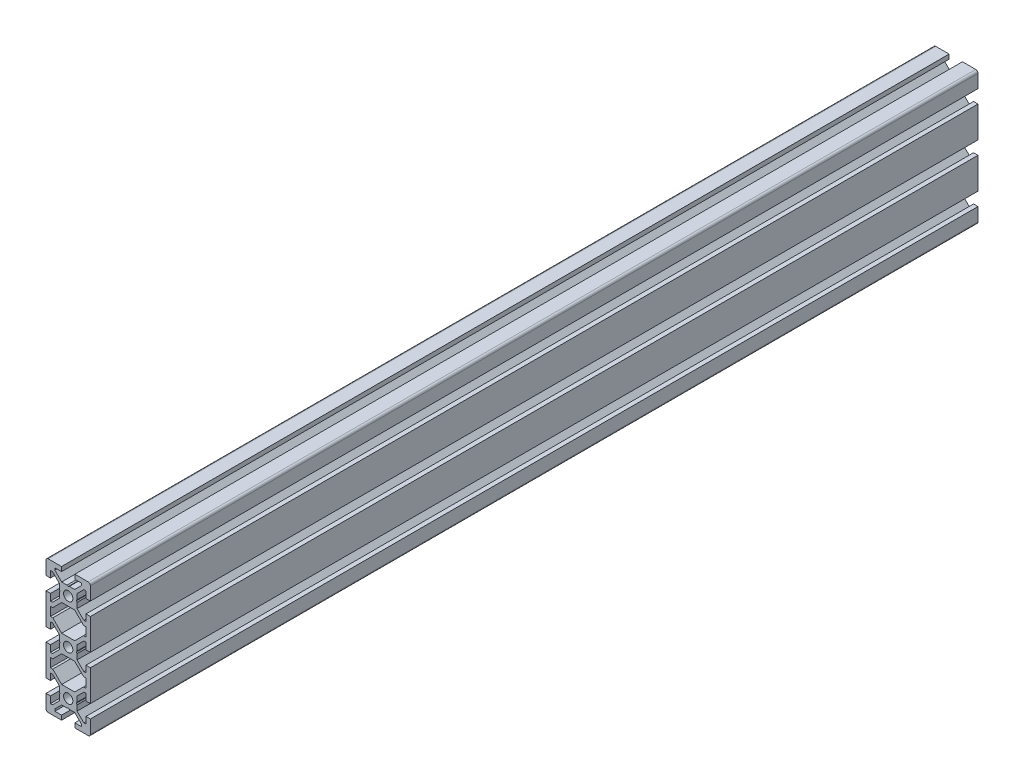
SolidWorks part; units mm, degrees
ref_plane "Front Plane" through (0, 0, 0) normal (0, 0, 1) x (1, 0, 0)
ref_plane "Top Plane" through (0, 0, 0) normal (0, 1, 0) x (1, 0, 0)
ref_plane "Right Plane" through (0, 0, 0) normal (1, 0, 0) x (0, 0, -1)
ref_plane "Plane1" through (0, 0, -400) normal (0, 0, -1) x (-1, 0, 0)
sketch "Sketch1" plane through (0, 0, -400) normal (0, 0, -1) x (-1, 0, 0)
  line L0 (6.9393, -8) -> (8, -8)
  line L1 (8, -8) -> (8, -12)
  line L2 (8, -12) -> (6.9393, -12)
  line L3 (6.9393, -12) -> (2.9393, -16)
  line L4 (2.9393, -16) -> (-2.9393, -16)
  line L5 (-2.9393, -16) -> (-6.9393, -12)
  line L6 (-6.9393, -12) -> (-8, -12)
  line L7 (-8, -12) -> (-8, -8)
  line L8 (-8, -8) -> (-6.9393, -8)
  line L9 (-6.9393, -8) -> (-2.9393, -4)
  line L10 (-2.9393, -4) -> (2.9393, -4)
  line L11 (2.9393, -4) -> (6.9393, -8)
  line L12 (8, 12) -> (8, 8)
  line L13 (8, 8) -> (6.9393, 8)
  line L14 (6.9393, 8) -> (2.9393, 4)
  line L15 (2.9393, 4) -> (-2.9393, 4)
  line L16 (-2.9393, 4) -> (-6.9393, 8)
  line L17 (-6.9393, 8) -> (-8, 8)
  line L18 (-8, 8) -> (-8, 12)
  line L19 (-8, 12) -> (-6.9393, 12)
  line L20 (-6.9393, 12) -> (-2.9393, 16)
  line L21 (-2.9393, 16) -> (2.9393, 16)
  line L22 (2.9393, 16) -> (6.9393, 12)
  line L23 (6.9393, 12) -> (8, 12)
  line L24 (10, -17) -> (10, -3)
  line L25 (10, -3) -> (8, -3)
  line L26 (8, -3) -> (8, -6)
  line L27 (8, -6) -> (7.0607, -6)
  line L28 (7.0607, -6) -> (4, -2.9393)
  line L29 (4, -2.9393) -> (4, -0.5196)
  line L30 (4, -0.5196) -> (3.7, 0)
  line L31 (3.7, 0) -> (4, 0.5196)
  line L32 (4, 0.5196) -> (4, 2.9393)
  line L33 (4, 2.9393) -> (7.0607, 6)
  line L34 (7.0607, 6) -> (8, 6)
  line L35 (8, 6) -> (8, 3)
  line L36 (8, 3) -> (10, 3)
  line L37 (10, 3) -> (10, 17)
  line L38 (10, 17) -> (8, 17)
  line L39 (8, 17) -> (8, 14)
  line L40 (8, 14) -> (7.0607, 14)
  line L41 (7.0607, 14) -> (4, 17.0607)
  line L42 (4, 17.0607) -> (4, 19.4804)
  line L43 (4, 19.4804) -> (3.7, 20)
  line L44 (3.7, 20) -> (4, 20.5196)
  line L45 (4, 20.5196) -> (4, 22.9393)
  line L46 (4, 22.9393) -> (7.0607, 26)
  line L47 (7.0607, 26) -> (8, 26)
  line L48 (8, 26) -> (8, 23)
  line L49 (8, 23) -> (10, 23)
  line L50 (10, 23) -> (10, 29)
  line L51 (9, 30) -> (3, 30)
  line L52 (3, 30) -> (3, 28)
  line L53 (3, 28) -> (6, 28)
  line L54 (6, 28) -> (6, 27.0607)
  line L55 (6, 27.0607) -> (2.9393, 24)
  line L56 (2.9393, 24) -> (0.5196, 24)
  line L57 (0.5196, 24) -> (0, 23.7)
  line L58 (0, 23.7) -> (-0.5196, 24)
  line L59 (-0.5196, 24) -> (-2.9393, 24)
  line L60 (-2.9393, 24) -> (-6, 27.0607)
  line L61 (-6, 27.0607) -> (-6, 28)
  line L62 (-6, 28) -> (-3, 28)
  line L63 (-3, 28) -> (-3, 30)
  line L64 (-3, 30) -> (-9, 30)
  line L65 (-10, 29) -> (-10, 23)
  line L66 (-10, 23) -> (-8, 23)
  line L67 (-8, 23) -> (-8, 26)
  line L68 (-8, 26) -> (-7.0607, 26)
  line L69 (-7.0607, 26) -> (-4, 22.9393)
  line L70 (-4, 22.9393) -> (-4, 20.5196)
  line L71 (-4, 20.5196) -> (-3.7, 20)
  line L72 (-3.7, 20) -> (-4, 19.4804)
  line L73 (-4, 19.4804) -> (-4, 17.0607)
  line L74 (-4, 17.0607) -> (-7.0607, 14)
  line L75 (-7.0607, 14) -> (-8, 14)
  line L76 (-8, 14) -> (-8, 17)
  line L77 (-8, 17) -> (-10, 17)
  line L78 (-10, 17) -> (-10, 3)
  line L79 (-10, 3) -> (-8, 3)
  line L80 (-8, 3) -> (-8, 6)
  line L81 (-8, 6) -> (-7.0607, 6)
  line L82 (-7.0607, 6) -> (-4, 2.9393)
  line L83 (-4, 2.9393) -> (-4, 0.5196)
  line L84 (-4, 0.5196) -> (-3.7, 0)
  line L85 (-3.7, 0) -> (-4, -0.5196)
  line L86 (-4, -0.5196) -> (-4, -2.9393)
  line L87 (-4, -2.9393) -> (-7.0607, -6)
  line L88 (-7.0607, -6) -> (-8, -6)
  line L89 (-8, -6) -> (-8, -3)
  line L90 (-8, -3) -> (-10, -3)
  line L91 (-10, -3) -> (-10, -17)
  line L92 (-10, -17) -> (-8, -17)
  line L93 (-8, -17) -> (-8, -14)
  line L94 (-8, -14) -> (-7.0607, -14)
  line L95 (-7.0607, -14) -> (-4, -17.0607)
  line L96 (-4, -17.0607) -> (-4, -19.4804)
  line L97 (-4, -19.4804) -> (-3.7, -20)
  line L98 (-3.7, -20) -> (-4, -20.5196)
  line L99 (-4, -20.5196) -> (-4, -22.9393)
  line L100 (-4, -22.9393) -> (-7.0607, -26)
  line L101 (-7.0607, -26) -> (-8, -26)
  line L102 (-8, -26) -> (-8, -23)
  line L103 (-8, -23) -> (-10, -23)
  line L104 (-10, -23) -> (-10, -29)
  line L105 (-9, -30) -> (-3, -30)
  line L106 (-3, -30) -> (-3, -28)
  line L107 (-3, -28) -> (-6, -28)
  line L108 (-6, -28) -> (-6, -27.0607)
  line L109 (-6, -27.0607) -> (-2.9393, -24)
  line L110 (-2.9393, -24) -> (-0.5196, -24)
  line L111 (-0.5196, -24) -> (0, -23.7)
  line L112 (0, -23.7) -> (0.5196, -24)
  line L113 (0.5196, -24) -> (2.9393, -24)
  line L114 (2.9393, -24) -> (6, -27.0607)
  line L115 (6, -27.0607) -> (6, -28)
  line L116 (6, -28) -> (3, -28)
  line L117 (3, -28) -> (3, -30)
  line L118 (3, -30) -> (9, -30)
  line L119 (10, -29) -> (10, -23)
  line L120 (10, -23) -> (8, -23)
  line L121 (8, -23) -> (8, -26)
  line L122 (8, -26) -> (7.0607, -26)
  line L123 (7.0607, -26) -> (4, -22.9393)
  line L124 (4, -22.9393) -> (4, -20.5196)
  line L125 (4, -20.5196) -> (3.7, -20)
  line L126 (3.7, -20) -> (4, -19.4804)
  line L127 (4, -19.4804) -> (4, -17.0607)
  line L128 (4, -17.0607) -> (7.0607, -14)
  line L129 (7.0607, -14) -> (8, -14)
  line L130 (8, -14) -> (8, -17)
  line L131 (8, -17) -> (10, -17)
  circle A0 centre (0, 0) radius 2.1
  circle A1 centre (0, -20) radius 2.1
  circle A2 centre (0, 20) radius 2.1
  arc A3 (10, 29) -> (9, 30) centre (9, 29) ccw
  arc A4 (-9, 30) -> (-10, 29) centre (-9, 29) ccw
  arc A5 (-10, -29) -> (-9, -30) centre (-9, -29) ccw
  arc A6 (9, -30) -> (10, -29) centre (9, -29) ccw
extrude "Boss-Extrude1" add sketch "Sketch1" against normal blind 400
hole_wizard "M5x0.8 Tapped Hole1" positions "Sketch2" profile "Sketch3" tap size "M5x0.8" standard "ANSI Metric"
sketch "Sketch2" plane through (0, 0, 0) normal (0, 0, 1) x (1, 0, 0)
  point P0 (0, 20)
  point P3 (0, 0)
  point P6 (0, -20)
sketch "Sketch3" plane through (0, 20, 0) normal (1, 0, 0) x (0, -1, 0)
  line L0 (0, 0) -> (0, 15.2618)
  line L1 (0, 15.2618) -> (2.1, 14)
  line L2 (2.1, 14) -> (2.1, 0)
  line L5 (2.1, 0) -> (0, 0)
  line L10 (0, 15.2618) -> (-2.1, 14) construction
  line L11 (0, -6.35) -> (0, 107.95) construction
  dimension "Tap Drill Dia." = 4.2
  dimension "Tap Drill Depth" = 14
  dimension "Drill Angle" = 118
hole_wizard "M5x0.8 Tapped Hole2" positions "Sketch4" profile "Sketch5" tap size "M5x0.8" standard "ANSI Metric"
sketch "Sketch4" plane through (0, 0, -400) normal (0, 0, -1) x (-1, 0, 0)
  point P0 (0, -20)
  point P3 (0, 0)
  point P6 (0, 20)
sketch "Sketch5" plane through (0, -20, -400) normal (1, 0, 0) x (0, 1, 0)
  line L0 (0, 0) -> (0, 15.2618)
  line L1 (0, 15.2618) -> (2.1, 14)
  line L2 (2.1, 14) -> (2.1, 0)
  line L5 (2.1, 0) -> (0, 0)
  line L10 (0, 15.2618) -> (-2.1, 14) construction
  line L11 (0, -6.35) -> (0, 107.95) construction
  dimension "Tap Drill Dia." = 4.2
  dimension "Tap Drill Depth" = 14
  dimension "Drill Angle" = 118
